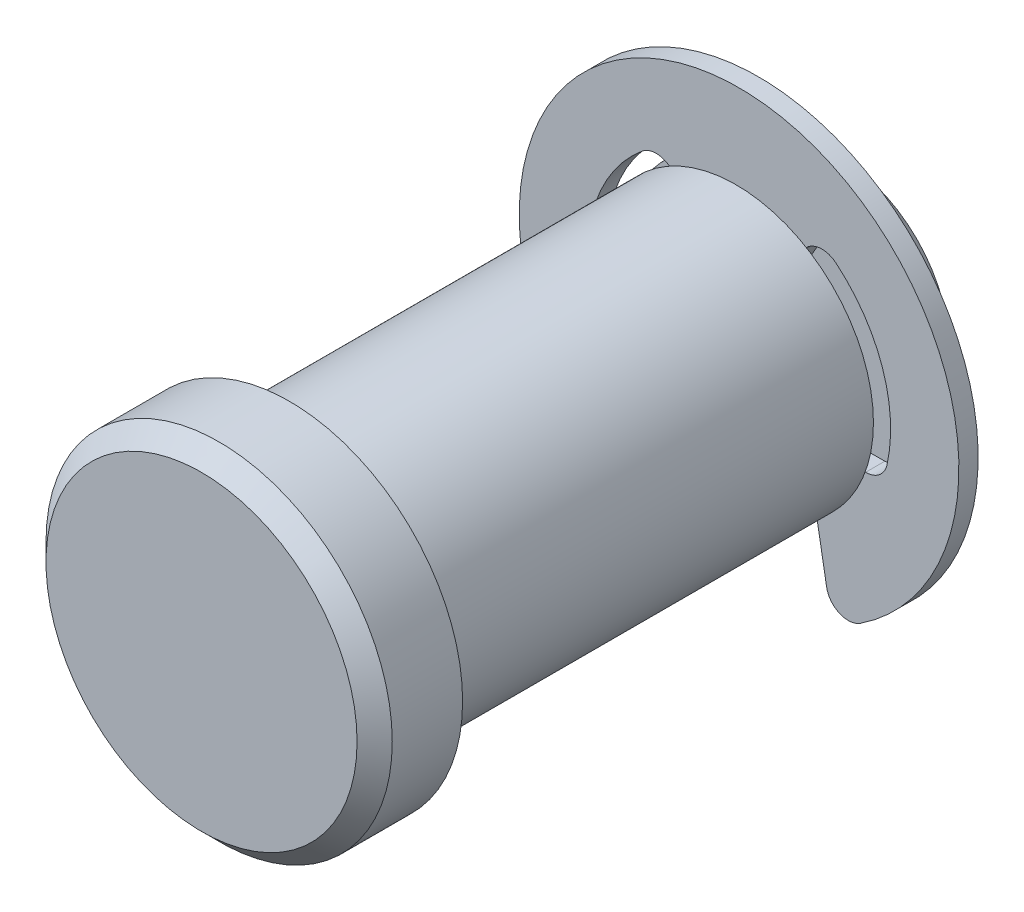
SolidWorks part; units mm, degrees
material "Water"
ref_plane "Front" through (0, 0, 0) normal (0, 0, 1) x (1, 0, 0)
ref_plane "Top" through (0, 0, 0) normal (0, 1, 0) x (1, 0, 0)
ref_plane "Right" through (0, 0, 0) normal (1, 0, 0) x (0, 0, -1)
sketch "Sketch2" plane through (0, 0, 0) normal (0, 0, 1) x (1, 0, 0)
  circle A0 centre (0, 0) radius 6.35
  point P3 (0, 6.35)
  point P4 (0, -6.35)
  dimension "dia" = 12.7
extrude "Extrude1" add sketch "Sketch2" along normal mid plane 25.4
sketch "Sketch3" plane through (0, 0, 0) normal (1, 0, 0) x (0, 0, -1)
  line L0 (12.7, 6.35) -> (-12.7, 6.35) construction
  line L1 (7.9375, 6.35) -> (9.1059, 6.35)
  line L2 (7.9375, 6.35) -> (7.9375, 3.8481)
  line L3 (7.9375, 3.8481) -> (9.1059, 3.8481)
  line L4 (9.1059, 6.35) -> (9.1059, 3.8481)
  line L5 (-12.7, 6.35) -> (-12.7, -6.35) construction
  line L10 (9.1059, 3.8481) -> (9.1059, -3.8481) construction
  point P11 (9.1059, 0)
  point P14 (8.5217, 6.35)
  dimension "groove wd" = 1.1684
  dimension "groove dia" = 7.6962
  dimension "usable lg" = 20.6375
revolve "Cut-Revolve1" cut sketch "Sketch3" angle 360 about axis through (0, 0, 12.7) along (0, 0, -1)
sketch "Sketch8" plane through (0, 0, 12.7) normal (0, 0, 1) x (1, 0, 0)
  circle A0 centre (0, 0) radius 8.001
  dimension "head dia" = 16.002
extrude "Extrude6" add sketch "Sketch8" along normal blind 4.064
chamfer "Chamfer2" distance 0.8128 angle 45 1 edges at (8.001, 0, 16.764)
ref_plane "Plane1" through (0, 0, -8.5217) normal (0, 0, 1) x (1, 0, 0)
sketch "Sketch4" plane through (0, 0, -8.5217) normal (0, 0, 1) x (1, 0, 0)
  line L0 (0, 3.8481) -> (0, -3.8481) construction
  circle A0 centre (0, 0) radius 10.16
  circle A1 centre (0, 0) radius 3.8481
  dimension "ring dia" = 20.32
extrude "Extrude2" add sketch "Sketch4" along normal mid plane 0.889 separate body
sketch "Sketch5" plane through (0, 0, 0) normal (0, 0, 1) x (1, 0, 0)
  line L0 (0, 10.16) -> (0, 3.8481) construction
  line L1 (-3.502, 6.0657) -> (0, 0)
  line L2 (-6.6126, -2.3089) -> (-3.0785, -2.3089)
  line L3 (0, 0) -> (3.502, 6.0657)
  line L4 (-3.0785, -2.3089) -> (-4.2949, -9.2076)
  line L5 (3.0785, -2.3089) -> (4.2949, -9.2076)
  line L6 (3.0785, -2.3089) -> (6.6126, -2.3089)
  arc A0 (-3.502, 6.0657) -> (-6.6126, -2.3089) centre (0, 0) ccw
  circle A1 centre (0, 0) radius 10.16 construction
  circle A2 centre (0, 0) radius 3.8481 construction
  arc A3 (6.6126, -2.3089) -> (3.502, 6.0657) centre (0, 0) ccw
  arc A4 (-4.2949, -9.2076) -> (4.2949, -9.2076) centre (0, 0) ccw
  circle A5 centre (0, 0) radius 3.8481 construction
  point P10 (0, 7.004)
  dimension "D1" = 30
  dimension "D2" = 10
  dimension "D3" = 2.3089
extrude "Extrude4" cut sketch "Sketch5" against normal through all
sketch "Sketch6" plane through (0, 0, -8.0772) normal (0, 0, 1) x (1, 0, 0)
  line L0 (-1.9241, 3.3326) -> (1.9241, 3.3326)
  circle A0 centre (0, 0) radius 3.8481 construction
  arc A1 (1.9241, 3.3326) -> (-1.9241, 3.3326) centre (0, 0) ccw
extrude "Extrude5" add sketch "Sketch6" against normal up to surface (0.889 mm away) up to face at (0, 1.215, -8.9662)
fillet "Fillet1" radius 1.016 6 edges at (4.2949, -9.2076, -8.5217) (-4.2949, -9.2076, -8.5217) (6.6126, -2.3089, -8.5217) (3.502, 6.0657, -8.5217) (-3.502, 6.0657, -8.5217) (-6.6126, -2.3089, -8.5217)
chamfer "Chamfer1" distance 1.27 angle 45 1 edges at (6.35, 0, -12.7)
sketch "Sketch7" plane through (0, 0, 0) normal (1, 0, 0) x (0, 0, -1)
  line L0 (8.9662, 10.16) -> (8.0772, 10.16) construction
  line L1 (12.7, -6.35) -> (12.7, 6.35) construction
  line L2 (8.0772, -8.6407) -> (8.9662, -8.6407) construction
  line L3 (-16.764, 7.1882) -> (-16.764, -7.1882) construction
  point P0 (9.1059, -8.6407)
  point P1 (12.7, 6.35)
  point P2 (-16.764, 8.001)
  point P6 (7.9375, 10.16)
  point P7 (12.7, -6.35)
  point P12 (-12.7, 8.001)
  point P16 (7.9375, -8.6407)
equation "\"D1@Chamfer1\" = \"dia@Sketch2\" * .1"
equation "\"D1@Fillet1\" = \"ring dia@Sketch4\" * .05"
equation "\"D3@Sketch5\" = \"groove dia@Sketch3\" * .3"
equation "\"D1@Chamfer2\" = \"head ht@Extrude6\" * .2"
